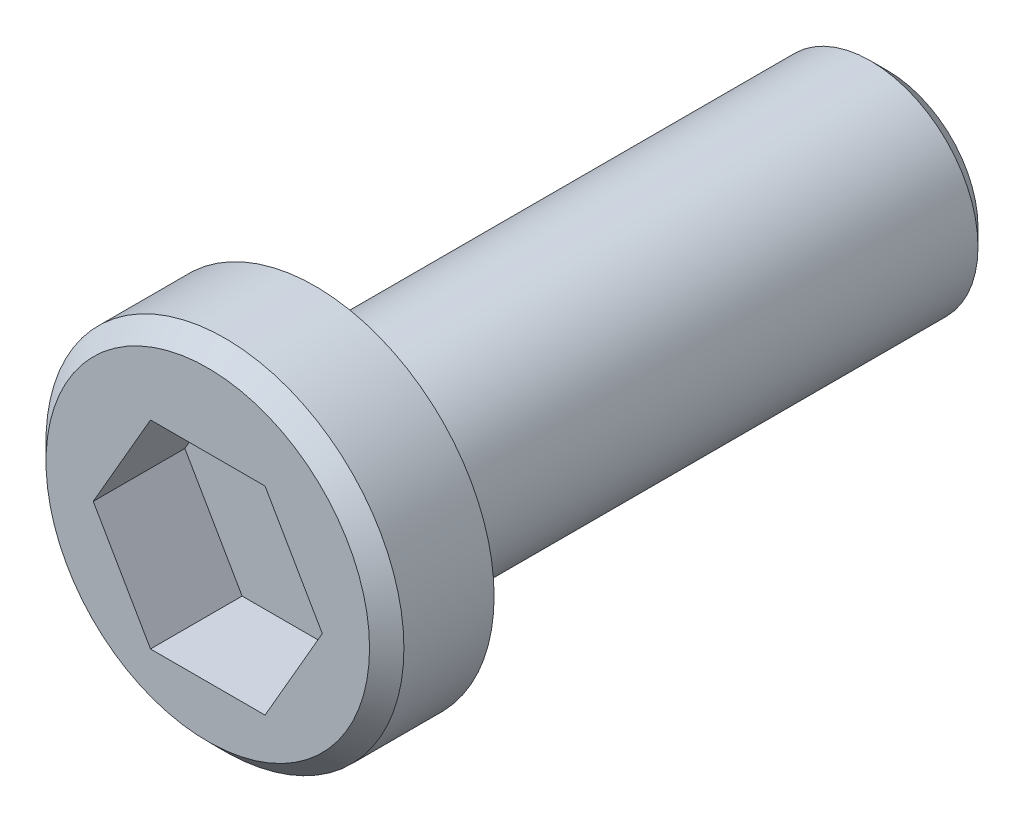
SolidWorks part; units mm, degrees
ref_plane "Front" through (0, 0, 0) normal (0, 0, 1) x (1, 0, 0)
ref_plane "Top" through (0, 0, 0) normal (0, 1, 0) x (1, 0, 0)
ref_plane "Right" through (0, 0, 0) normal (1, 0, 0) x (0, 0, -1)
sketch "Sketch1" plane through (0, 0, 0) normal (0, 0, 1) x (1, 0, 0)
  circle A0 centre (0, 0) radius 4.7625
  dimension "D1" = 9.525
extrude "Extrude1" add sketch "Sketch1" along normal blind 25.4
sketch "Sketch3" plane through (0, 0, 25.4) normal (0, 0, 1) x (1, 0, 0)
  circle A0 centre (0, 0.4916) radius 7.9375
  dimension "D1" = 15.875
extrude "Extrude3" add sketch "Sketch3" along normal blind 4.7625
chamfer "Chamfer1" distance 0.762 angle 45
sketch "Sketch4" plane through (0, 0, 30.1625) normal (0, 0, 1) x (1, 0, 0)
  line L0 (8.3344, 0) -> (-8.3344, 0) construction
  line L1 (5.08, 0) -> (2.54, 4.3994)
  line L2 (2.54, 4.3994) -> (-2.54, 4.3994)
  line L3 (-2.54, 4.3994) -> (-5.08, 0)
  line L4 (-5.08, 0) -> (-2.54, -4.3994)
  line L5 (-2.54, -4.3994) -> (2.54, -4.3994)
  line L6 (2.54, -4.3994) -> (5.08, 0)
  circle A0 centre (0, 0) radius 4.3994 construction
  dimension "D1" = 5.08
extrude "Cut-Extrude1" cut sketch "Sketch4" against normal blind 4.064
